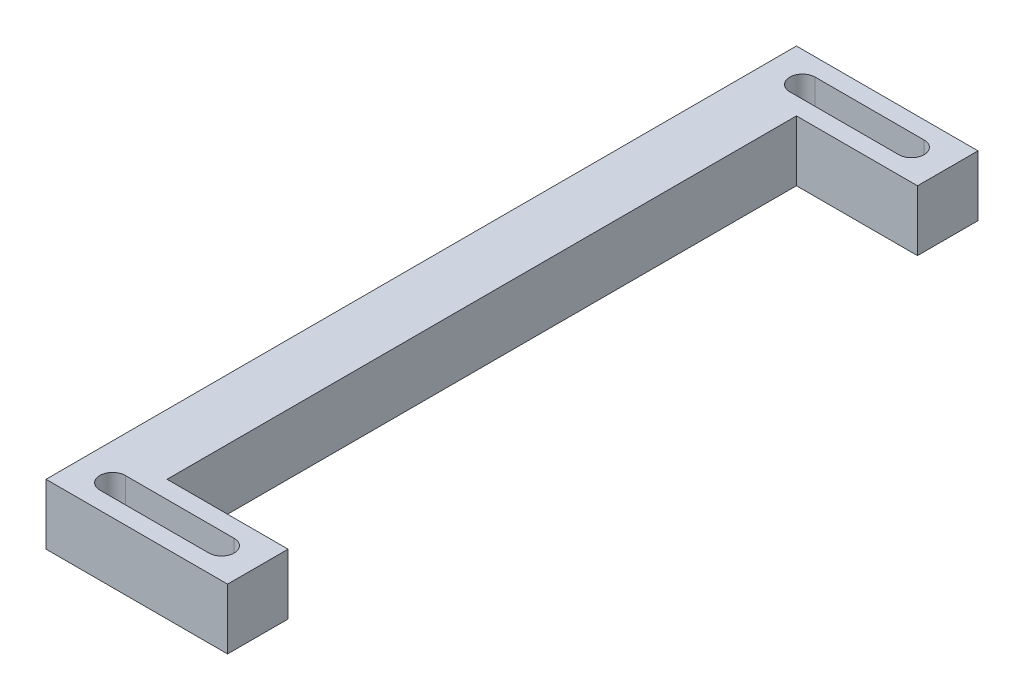
SolidWorks part; units mm, degrees
ref_plane "Plan de face" through (0, 0, 0) normal (0, 0, 1) x (1, 0, 0)
ref_plane "Plan de dessus" through (0, 0, 0) normal (0, 1, 0) x (1, 0, 0)
ref_plane "Plan de droite" through (0, 0, 0) normal (1, 0, 0) x (0, 0, -1)
sketch "Esquisse5" plane through (0, 0, 0) normal (0, 1, 0) x (1, 0, 0)
  line L0 (-87, 62) -> (-77, 52) construction
  line L1 (77, 52) -> (-77, 52) construction
  line L2 (77, 52) -> (77, -52) construction
  line L3 (77, -52) -> (-77, -52) construction
  line L4 (-77, 52) -> (-77, -52) construction
  line L5 (77, 52) -> (-77, -52) construction
  line L6 (77, -52) -> (-77, 52) construction
  line L7 (87, 62) -> (-87, 62) construction
  line L8 (87, 62) -> (87, -62) construction
  line L9 (87, -62) -> (-87, -62) construction
  line L10 (-87, 62) -> (-87, -62) construction
  line L11 (87, 62) -> (-87, -62) construction
  line L12 (87, -62) -> (-87, 62) construction
  line L13 (0, 0) -> (-139.4589, 0) construction
  line L14 (-81, 57) -> (-63, 57) construction
  line L15 (-81, 59.1) -> (-63, 59.1)
  line L16 (-57, 52) -> (-57, 62)
  line L17 (-57, 62) -> (-87, 62)
  line L18 (-87, 62) -> (-87, -62)
  line L19 (-87, -62) -> (-57, -62)
  line L20 (-57, -62) -> (-57, -52)
  line L21 (-57, -52) -> (-77, -52)
  line L22 (-77, -52) -> (-77, 52)
  line L23 (-77, 52) -> (-57, 52)
  line L24 (-81, 54.9) -> (-63, 54.9)
  line L25 (-81, -57) -> (-63, -57) construction
  line L26 (-81, -59.1) -> (-63, -59.1)
  line L27 (-81, -54.9) -> (-63, -54.9)
  arc A2 (-81, 59.1) -> (-81, 54.9) centre (-81, 57) ccw
  arc A3 (-63, 54.9) -> (-63, 59.1) centre (-63, 57) ccw
  arc A4 (-81, -59.1) -> (-81, -54.9) centre (-81, -57) cw
  arc A5 (-63, -54.9) -> (-63, -59.1) centre (-63, -57) cw
  point P2 (0, 0)
  point P4 (0, 0)
  point P20 (-72, 57)
  point P27 (-72, 62)
  point P29 (-57, 57)
  point P32 (-72, -57)
  dimension "D7" = 18
  dimension "D6" = 2.1
  dimension "D1" = 104
  dimension "D2" = 124
  dimension "D3" = 154
  dimension "D4" = 174
  dimension "D5" = 20
extrude "Boss.-Extru.3" add sketch "Esquisse5" along normal blind 10
